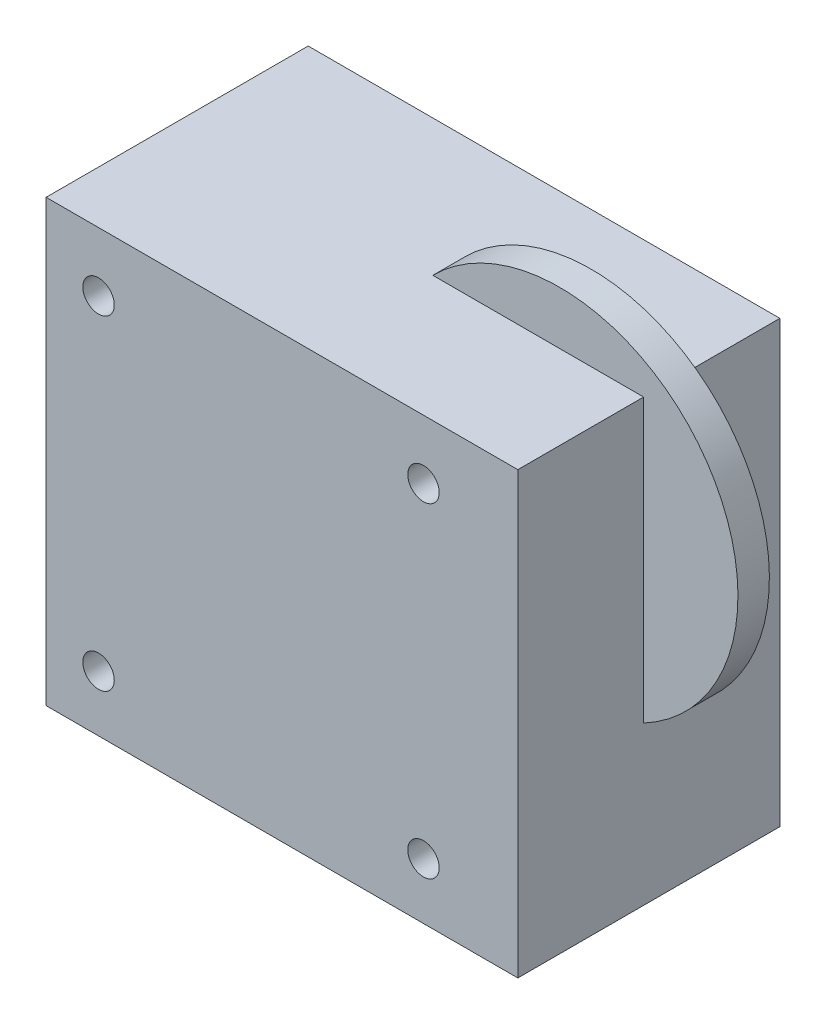
SolidWorks part; units mm, degrees
material "ABS"
ref_plane "Front Plane" through (0, 0, 0) normal (0, 0, 1) x (1, 0, 0)
ref_plane "Top Plane" through (0, 0, 0) normal (0, 1, 0) x (1, 0, 0)
ref_plane "Right Plane" through (0, 0, 0) normal (1, 0, 0) x (0, 0, -1)
sketch "Sketch1" plane through (0, 0, 0) normal (0, 0, 1) x (1, 0, 0)
  line L1 (-22.5, -21) -> (22.5, -21)
  line L2 (-22.5, -21) -> (-22.5, 21)
  line L3 (-22.5, 21) -> (22.5, 21)
  line L4 (22.5, -21) -> (22.5, 21)
  line L5 (-22.5, -21) -> (22.5, 21) construction
  line L6 (-22.5, 21) -> (22.5, -21) construction
  point P0 (0, 0)
  dimension "D1" = 45
  dimension "D2" = 42
extrude "Boss-Extrude1" add sketch "Sketch1" along normal blind 25
sketch "Sketch2" plane through (0, 0, 25) normal (0, 0, 1) x (1, 0, 0)
  line L0 (-22.5, 21) -> (-22.5, -21) construction
  circle A0 centre (13.5, 15.35) radius 1.5
  circle A1 centre (-17.5, 15.35) radius 1.5
  circle A2 centre (-17.5, -15.65) radius 1.5
  circle A3 centre (13.5, -15.65) radius 1.5
  dimension "D1" = 3
  dimension "D2" = 3
  dimension "D3" = 3
  dimension "D4" = 3
  dimension "D5" = 5
  dimension "D6" = 5
  dimension "D7" = 31
  dimension "D8" = 31
  dimension "D9" = 31
extrude "Cut-Extrude1" cut sketch "Sketch2" against normal through all
ref_plane "Plane1" through (0, 0, 10) normal (0, 0, 1) x (1, 0, 0)
sketch "Sketch3" plane through (0, 0, 10) normal (0, 0, 1) x (1, 0, 0)
  line L2 (31.5, 9.0644) -> (-2.5, 9.0644) construction
  line L3 (22.5, -21) -> (22.5, 21) construction
  circle A0 centre (14.5, 9.0644) radius 17
  dimension "D1" = 34
  dimension "D2" = 9
extrude "Boss-Extrude2" add sketch "Sketch3" along normal blind 3
ref_plane "Plane2" through (22.5, 21, 13) normal (-1, 0, 0) x (0, 0, 1)
